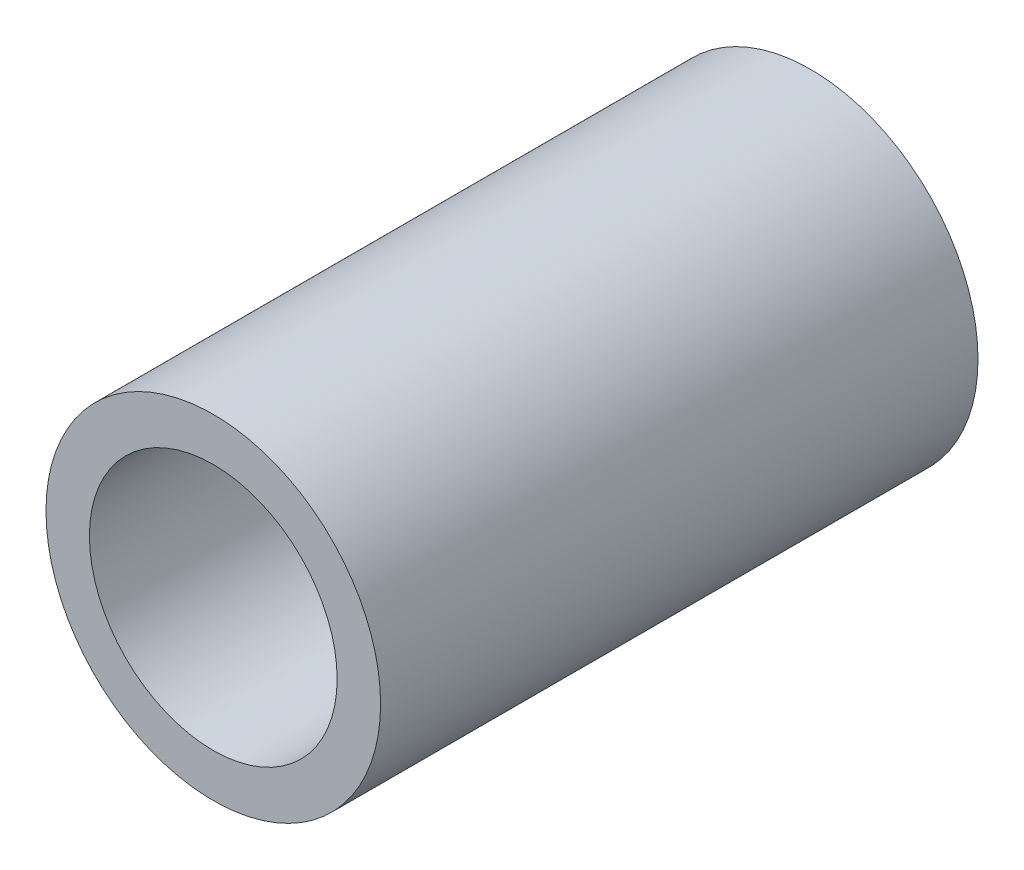
SolidWorks part; units mm, degrees
ref_plane "Front Plane" through (0, 0, 0) normal (0, 0, 1) x (1, 0, 0)
ref_plane "Top Plane" through (0, 0, 0) normal (0, 1, 0) x (1, 0, 0)
ref_plane "Right Plane" through (0, 0, 0) normal (1, 0, 0) x (0, 0, -1)
sketch "Sketch1" plane through (0, 0, 0) normal (0, 0, 1) x (1, 0, 0)
  circle A0 centre (0, 0) radius 10.668
  dimension "Pipe OD" = 21.336
extrude "Extrude-Thin1" add sketch "Sketch1" along normal mid plane 38.1 thin thin type one direction reverse wall 2.7686
